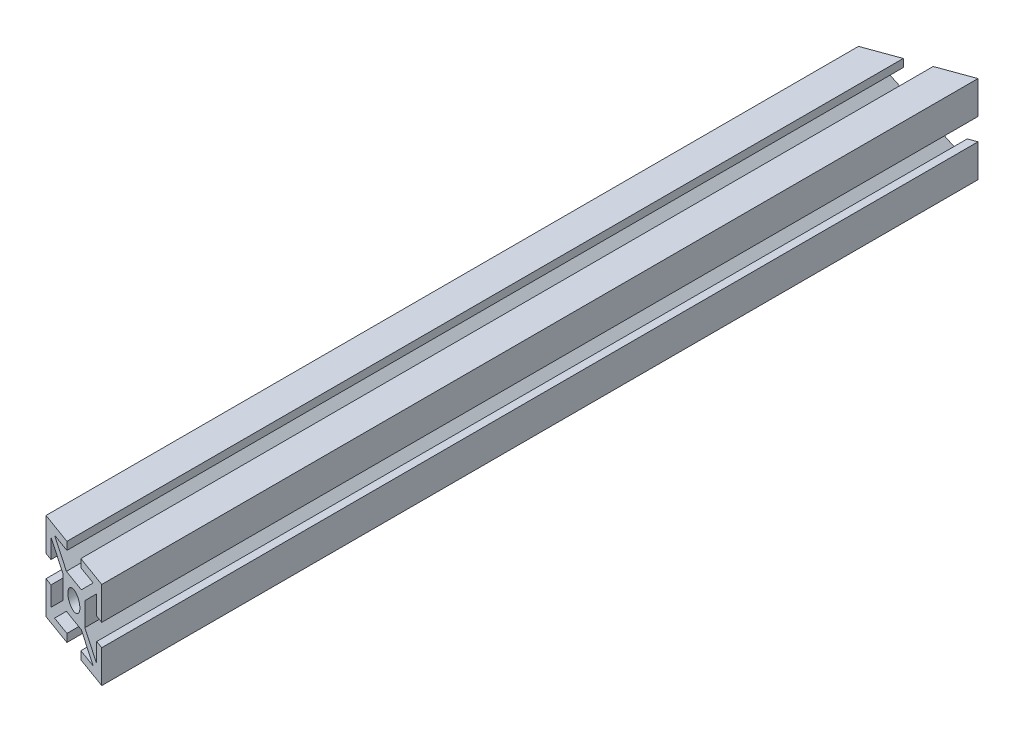
SolidWorks part; units mm, degrees
material "6063-T5"
ref_plane "Front Plane" through (0, 0, 0) normal (0, 0, 1) x (1, 0, 0)
ref_plane "Top Plane" through (0, 0, 0) normal (0, 1, 0) x (1, 0, 0)
ref_plane "Right Plane" through (0, 0, 0) normal (1, 0, 0) x (0, 0, -1)
sketch "Sketch2" plane through (0, 0, 0) normal (0, 0, 1) x (1, 0, 0)
  line L0 (-2.5, 10) -> (-2.5, 8.2)
  line L1 (-10, -10) -> (-2.5, -10)
  line L2 (-10, -10) -> (-10, -2.5)
  line L3 (-10, 10) -> (-2.5, 10)
  line L4 (10, -10) -> (10, -2.5)
  line L5 (-10, -10) -> (10, 10) construction
  line L6 (-10, 10) -> (10, -10) construction
  line L7 (-6.9272, -8.2) -> (-2.5, -8.2)
  line L8 (-8.2, -6.9272) -> (-8.2, -2.5)
  line L9 (-6.9272, 8.2) -> (-2.5, 8.2)
  line L10 (8.2, -6.9272) -> (8.2, -2.5)
  line L13 (2.5, 10) -> (2.5, 8.2)
  line L14 (2.5, 10) -> (10, 10)
  line L15 (2.5, 8.2) -> (6.9272, 8.2)
  line L16 (0, 0) -> (0, 17.5125) construction
  line L17 (-2.15, 2.15) -> (2.15, 2.15) construction
  line L18 (-2.6772, -3.95) -> (2.6772, -3.95)
  line L19 (-3.95, -2.6772) -> (-3.95, 2.6772)
  line L20 (-2.6772, 3.95) -> (2.6772, 3.95)
  line L21 (3.95, -2.6772) -> (3.95, 2.6772)
  line L24 (-2.6772, 3.95) -> (-6.9272, 8.2)
  line L25 (-3.95, 2.6772) -> (-8.2, 6.9272)
  line L26 (10, 2.5) -> (8.2, 2.5)
  line L27 (10, -2.5) -> (8.2, -2.5)
  line L28 (3.95, 2.6772) -> (8.2, 6.9272)
  line L29 (2.6772, 3.95) -> (6.9272, 8.2)
  line L30 (2.5, -10) -> (2.5, -8.2)
  line L31 (-2.5, -10) -> (-2.5, -8.2)
  line L32 (2.6772, -3.95) -> (6.9272, -8.2)
  line L33 (3.95, -2.6772) -> (8.2, -6.9272)
  line L34 (-10, -2.5) -> (-8.2, -2.5)
  line L35 (-10, 2.5) -> (-8.2, 2.5)
  line L36 (-3.95, -2.6772) -> (-8.2, -6.9272)
  line L37 (-2.6772, -3.95) -> (-6.9272, -8.2)
  line L38 (-10, 2.5) -> (-10, 10)
  line L39 (-8.2, 2.5) -> (-8.2, 6.9272)
  line L40 (10, 2.5) -> (10, 10)
  line L41 (8.2, 2.5) -> (8.2, 6.9272)
  line L42 (2.5, -8.2) -> (6.9272, -8.2)
  line L43 (2.5, -10) -> (10, -10)
  circle A0 centre (0, 0) radius 2.15
  point P0 (0, 0)
  point P54 (0, 0)
  dimension "D3" = 4.3
  dimension "D7" = 1.8
  dimension "D1" = 20
  dimension "D4" = 1.8
  dimension "D5" = 5
  dimension "D6" = 1.8
  dimension "D8" = 4
extrude "Boss-Extrude1" add sketch "Sketch2" along normal mid plane 200
sketch "Sketch3" plane through (0, 10, 0) normal (0, 1, 0) x (1, 0, 0)
  line L0 (-10, -100) -> (10, -100)
  line L1 (10, -100) -> (-10, -92.7206)
  line L2 (-10, -100) -> (-10, 100) construction
  line L3 (-10, -92.7206) -> (-10, -100)
  dimension "D1" = 20
extrude "Cut-Extrude1" cut sketch "Sketch3" against normal through all
sketch "Sketch4" plane through (0, 10, 0) normal (0, 1, 0) x (1, 0, 0)
  line L0 (10, 100) -> (-10, 100)
  line L1 (-10, 100) -> (-10, 92.7206)
  line L2 (-10, -92.7206) -> (-10, 100) construction
  line L3 (-10, 92.7206) -> (10, 100)
  dimension "D1" = 20
extrude "Cut-Extrude2" cut sketch "Sketch4" against normal through all
